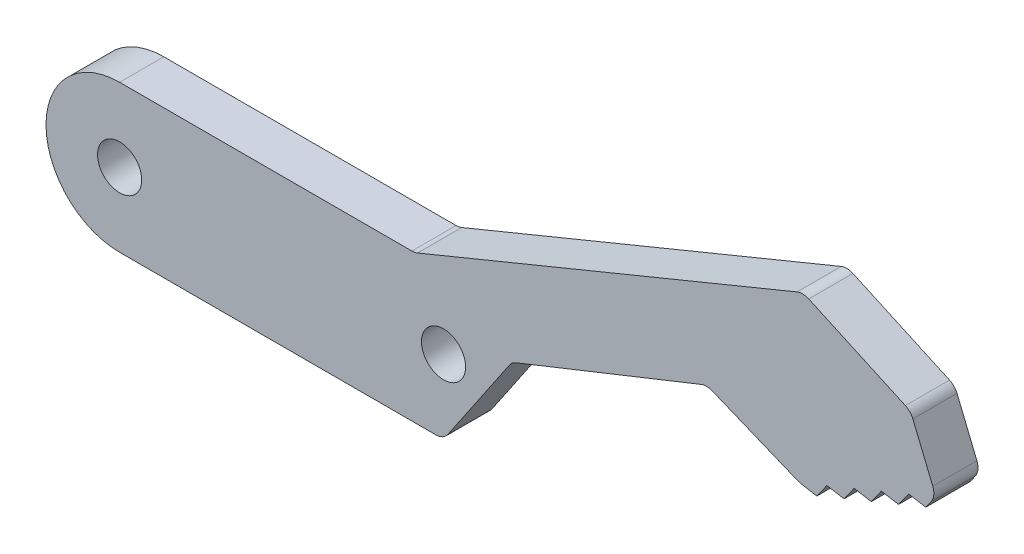
SolidWorks part; units mm, degrees
ref_plane "Front Plane" through (0, 0, 0) normal (0, 0, 1) x (1, 0, 0)
ref_plane "Top Plane" through (0, 0, 0) normal (0, 1, 0) x (1, 0, 0)
ref_plane "Right Plane" through (0, 0, 0) normal (1, 0, 0) x (0, 0, -1)
sketch "Sketch1" plane through (0, 0, 0) normal (0, 0, 1) x (1, 0, 0)
  line L0 (0, 0) -> (22, 0) construction
  line L1 (0, 5) -> (22, 5)
  line L2 (0, -5) -> (22, -5)
  line L3 (20.05, 5) -> (23.9914, -4.5863) construction
  line L4 (20.05, 5) -> (51.4959, 17.929) construction
  line L5 (23.9914, -4.5863) -> (55.4373, 8.3426) construction
  line L6 (51.4959, 17.929) -> (55.4373, 8.3426) construction
  line L7 (20.05, 5) -> (46.409, 15.8375)
  line L8 (46.409, 15.8375) -> (53.7261, 12.5046)
  line L9 (53.7261, 12.5046) -> (55.4373, 8.3426)
  line L10 (55.4373, 8.3426) -> (46.1885, 4.54) construction
  line L11 (46.1885, 4.54) -> (39.8718, 7.1258)
  line L12 (39.8718, 7.1258) -> (26.6444, 1.8518)
  line L13 (46.1885, 4.54) -> (47.3529, 4.3376)
  line L14 (47.3529, 4.3376) -> (48.0382, 5.3005)
  line L15 (47.3529, 4.3376) -> (54.752, 7.3797) construction
  line L16 (48.0382, 5.3005) -> (49.2027, 5.0981)
  line L17 (49.2027, 5.0981) -> (49.888, 6.0611)
  line L18 (49.888, 6.0611) -> (51.0524, 5.8587)
  line L19 (51.0524, 5.8587) -> (51.7378, 6.8216)
  line L20 (51.7378, 6.8216) -> (52.9022, 6.6192)
  line L21 (52.9022, 6.6192) -> (53.5875, 7.5821)
  line L22 (53.5875, 7.5821) -> (54.752, 7.3797)
  line L23 (54.752, 7.3797) -> (55.4373, 8.3426)
  line L24 (26.6444, 1.8518) -> (22, -5)
  arc A0 (0, 5) -> (0, -5) centre (0, 0) ccw
  arc A1 (22, -5) -> (22, 5) centre (22, 0) ccw
  circle A2 centre (0, 0) radius 1.5
  circle A3 centre (22, 0) radius 1.5
  point P3 (11, 0)
  dimension "D2" = 10
  dimension "D11" = 3
  dimension "D1" = 22
  dimension "D3" = 157.65
  dimension "D4" = 1.95
  dimension "D5" = 34
  dimension "D6" = 136
  dimension "D7" = 10
  dimension "D8" = 4.5
  dimension "D9" = 5.5
  dimension "D10" = 14.24
  dimension "D12" = 2
  dimension "D13" = 0.63
  dimension "D14" = 8
extrude "Boss-Extrude1" add sketch "Sketch1" along normal blind 3 contours L24 A1 L1 A0 L2 A3 A2 | A1 L12 L11 L13 L14 L16 L17 L18 L19 L20 L21 L22 L23 L9 L8 L7 L1
fillet "Fillet1" radius 1 8 edges at (26.6444, 1.8518, 1.5) (22, -5, 1.5) (39.8718, 7.1258, 1.5) (46.1885, 4.54, 1.5) (55.4373, 8.3426, 1.5) (53.7261, 12.5046, 1.5) (46.409, 15.8375, 1.5) (20.05, 5, 1.5)
